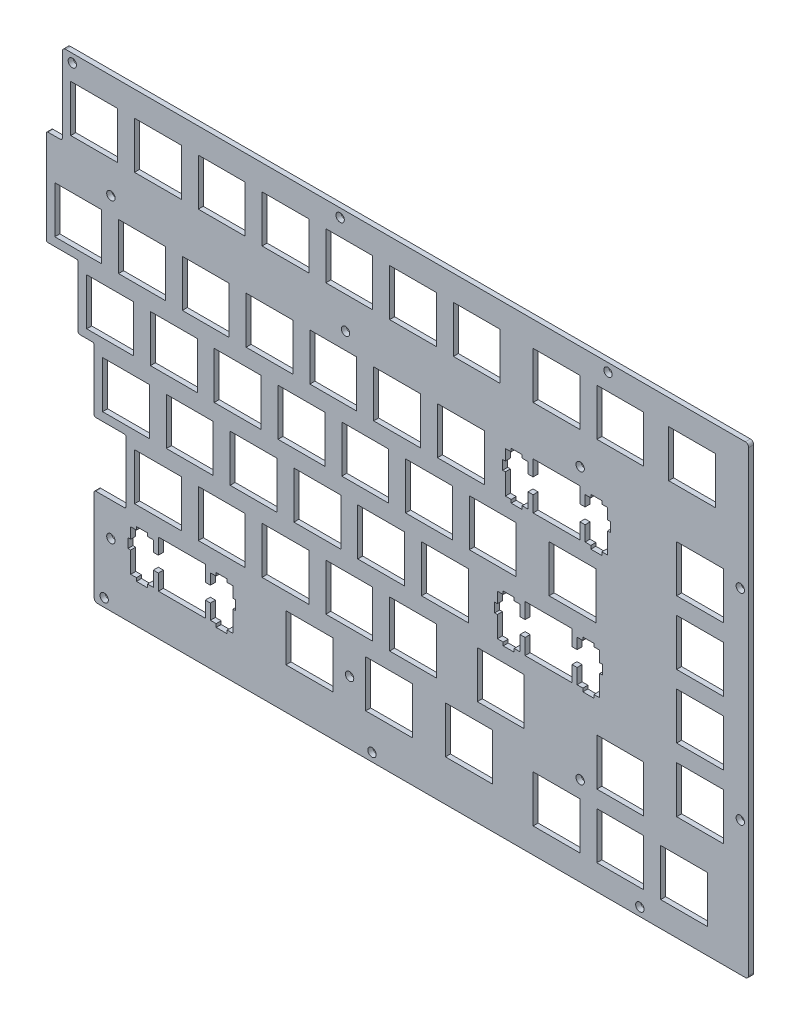
SolidWorks part; units mm, degrees
material "PC 高粘度"
ref_plane "前视基准面" through (0, 0, 0) normal (0, 0, 1) x (1, 0, 0)
ref_plane "上视基准面" through (0, 0, 0) normal (0, 1, 0) x (1, 0, 0)
ref_plane "右视基准面" through (0, 0, 0) normal (1, 0, 0) x (0, 0, -1)
other "Configuration Table"
sketch "Model" plane through (0, 0, 0) normal (0, 0, 1) x (1, 0, 0)
  line L0 (4.8569, 129.021) -> (204.883, 129.021)
  line L1 (204.883, 129.021) -> (204.883, 0.4341)
  line L2 (204.883, 0.4341) -> (14.3819, 0.4341)
  line L3 (21.3817, 112.498) -> (7.3822, 126.497) construction
  line L4 (145.495, 16.9595) -> (159.494, 16.9595)
  line L5 (159.494, 16.9595) -> (159.494, 2.96)
  line L6 (159.494, 2.96) -> (145.495, 2.96)
  line L7 (145.495, 2.96) -> (145.495, 16.9595)
  line L8 (164.545, 16.9595) -> (178.544, 16.9595)
  line L9 (178.544, 16.9595) -> (178.544, 2.96)
  line L10 (178.544, 2.96) -> (164.545, 2.96)
  line L11 (164.545, 2.96) -> (164.545, 16.9595)
  line L12 (183.595, 16.9595) -> (197.594, 16.9595)
  line L13 (197.594, 16.9595) -> (197.594, 2.96)
  line L14 (197.594, 2.96) -> (183.595, 2.96)
  line L15 (183.595, 2.96) -> (183.595, 16.9595)
  line L16 (33.5759, 21.722) -> (33.5759, 17.0215)
  line L17 (33.5759, 17.0215) -> (32.0504, 17.0215)
  line L18 (32.0504, 17.0215) -> (32.0504, 20.2517)
  line L19 (32.0504, 20.2517) -> (30.3251, 20.2517)
  line L20 (30.3251, 20.2517) -> (30.3251, 21.1722)
  line L21 (30.3251, 21.1722) -> (27.0261, 21.1722)
  line L22 (27.0261, 21.1722) -> (27.0261, 20.2517)
  line L23 (27.0261, 20.2517) -> (25.3008, 20.2517)
  line L24 (25.3008, 20.2517) -> (25.3008, 17.0215)
  line L25 (25.3008, 17.0215) -> (24.4753, 17.0215)
  line L26 (24.4753, 17.0215) -> (24.4753, 14.2227)
  line L27 (24.4753, 14.2227) -> (25.3008, 14.2227)
  line L28 (25.3008, 14.2227) -> (25.3008, 7.9527)
  line L29 (25.3008, 7.9527) -> (27.0261, 7.9527)
  line L30 (27.0261, 7.9527) -> (27.0261, 6.9729)
  line L31 (27.0261, 6.9729) -> (30.3251, 6.9729)
  line L32 (30.3251, 6.9729) -> (30.3251, 7.9527)
  line L33 (30.3251, 7.9527) -> (32.0504, 7.9527)
  line L34 (32.0504, 7.9527) -> (32.0504, 12.4216)
  line L35 (32.0504, 12.4216) -> (33.5759, 12.4216)
  line L36 (33.5759, 12.4216) -> (33.5759, 7.7225)
  line L37 (33.5759, 7.7225) -> (47.5753, 7.7225)
  line L38 (47.5753, 7.7225) -> (47.5753, 12.4216)
  line L39 (47.5753, 12.4216) -> (49.101, 12.4216)
  line L40 (49.101, 12.4216) -> (49.101, 7.9527)
  line L41 (49.101, 7.9527) -> (50.8247, 7.9527)
  line L42 (50.8247, 7.9527) -> (50.8247, 6.9729)
  line L43 (50.8247, 6.9729) -> (54.1253, 6.9729)
  line L44 (54.1253, 6.9729) -> (54.1253, 7.9527)
  line L45 (54.1253, 7.9527) -> (55.8504, 7.9527)
  line L46 (55.8504, 7.9527) -> (55.8504, 14.2227)
  line L47 (55.8504, 14.2227) -> (56.6759, 14.2227)
  line L48 (56.6759, 14.2227) -> (56.6759, 17.0215)
  line L49 (56.6759, 17.0215) -> (55.8504, 17.0215)
  line L50 (55.8504, 17.0215) -> (55.8504, 20.2517)
  line L51 (55.8504, 20.2517) -> (54.1253, 20.2517)
  line L52 (54.1253, 20.2517) -> (54.1253, 21.1722)
  line L53 (54.1253, 21.1722) -> (50.8247, 21.1722)
  line L54 (50.8247, 21.1722) -> (50.8247, 20.2517)
  line L55 (50.8247, 20.2517) -> (49.101, 20.2517)
  line L56 (49.101, 20.2517) -> (49.101, 17.0215)
  line L57 (49.101, 17.0215) -> (47.5753, 17.0215)
  line L58 (47.5753, 17.0215) -> (47.5753, 21.722)
  line L59 (47.5753, 21.722) -> (33.5759, 21.722)
  line L60 (71.676, 21.722) -> (85.6753, 21.722)
  line L61 (85.6753, 21.722) -> (85.6753, 7.7225)
  line L62 (85.6753, 7.7225) -> (71.676, 7.7225)
  line L63 (71.676, 7.7225) -> (71.676, 21.722)
  line L64 (95.4871, 21.722) -> (109.488, 21.722)
  line L65 (109.488, 21.722) -> (109.488, 7.7225)
  line L66 (109.488, 7.7225) -> (95.4871, 7.7225)
  line L67 (95.4871, 7.7225) -> (95.4871, 21.722)
  line L68 (119.301, 21.722) -> (133.3, 21.722)
  line L69 (133.3, 21.722) -> (133.3, 7.7225)
  line L70 (133.3, 7.7225) -> (119.301, 7.7225)
  line L71 (119.301, 7.7225) -> (119.301, 21.722)
  line L72 (164.545, 36.0094) -> (178.544, 36.0094)
  line L73 (178.544, 36.0094) -> (178.544, 22.01)
  line L74 (178.544, 22.01) -> (164.545, 22.01)
  line L75 (164.545, 22.01) -> (164.545, 36.0094)
  line L76 (26.4322, 40.7719) -> (40.4315, 40.7719)
  line L77 (40.4315, 40.7719) -> (40.4315, 26.7725)
  line L78 (40.4315, 26.7725) -> (26.4322, 26.7725)
  line L79 (26.4322, 26.7725) -> (26.4322, 40.7719)
  line L80 (45.4822, 40.7719) -> (59.4815, 40.7719)
  line L81 (59.4815, 40.7719) -> (59.4815, 26.7725)
  line L82 (59.4815, 26.7725) -> (45.4822, 26.7725)
  line L83 (45.4822, 26.7725) -> (45.4822, 40.7719)
  line L84 (64.5322, 40.7719) -> (78.5315, 40.7719)
  line L85 (78.5315, 40.7719) -> (78.5315, 26.7725)
  line L86 (78.5315, 26.7725) -> (64.5322, 26.7725)
  line L87 (64.5322, 26.7725) -> (64.5322, 40.7719)
  line L88 (83.5822, 40.7719) -> (97.5815, 40.7719)
  line L89 (97.5815, 40.7719) -> (97.5815, 26.7725)
  line L90 (97.5815, 26.7725) -> (83.5822, 26.7725)
  line L91 (83.5822, 26.7725) -> (83.5822, 40.7719)
  line L92 (102.632, 40.7719) -> (116.632, 40.7719)
  line L93 (116.632, 40.7719) -> (116.632, 26.7725)
  line L94 (116.632, 26.7725) -> (102.632, 26.7725)
  line L95 (102.632, 26.7725) -> (102.632, 40.7719)
  line L96 (128.826, 40.7719) -> (142.825, 40.7719)
  line L97 (142.825, 40.7719) -> (142.825, 26.7725)
  line L98 (142.825, 26.7725) -> (128.826, 26.7725)
  line L99 (128.826, 26.7725) -> (128.826, 40.7719)
  line L100 (188.357, 40.7719) -> (202.357, 40.7719)
  line L101 (202.357, 40.7719) -> (202.357, 26.7725)
  line L102 (202.357, 26.7725) -> (188.357, 26.7725)
  line L103 (188.357, 26.7725) -> (188.357, 40.7719)
  line L104 (143.112, 59.8219) -> (143.112, 55.1215)
  line L105 (143.112, 55.1215) -> (141.588, 55.1215)
  line L106 (141.588, 55.1215) -> (141.588, 58.3516)
  line L107 (141.588, 58.3516) -> (139.863, 58.3516)
  line L108 (139.863, 58.3516) -> (139.863, 59.2723)
  line L109 (139.863, 59.2723) -> (136.562, 59.2723)
  line L110 (136.562, 59.2723) -> (136.562, 58.3516)
  line L111 (136.562, 58.3516) -> (134.837, 58.3516)
  line L112 (134.837, 58.3516) -> (134.837, 55.1215)
  line L113 (134.837, 55.1215) -> (134.013, 55.1215)
  line L114 (134.013, 55.1215) -> (134.013, 52.3226)
  line L115 (134.013, 52.3226) -> (134.837, 52.3226)
  line L116 (134.837, 52.3226) -> (134.837, 46.0527)
  line L117 (134.837, 46.0527) -> (136.562, 46.0527)
  line L118 (136.562, 46.0527) -> (136.562, 45.0716)
  line L119 (136.562, 45.0716) -> (139.863, 45.0716)
  line L120 (139.863, 45.0716) -> (139.863, 46.0527)
  line L121 (139.863, 46.0527) -> (141.588, 46.0527)
  line L122 (141.588, 46.0527) -> (141.588, 50.5217)
  line L123 (141.588, 50.5217) -> (143.112, 50.5217)
  line L124 (143.112, 50.5217) -> (143.112, 45.8227)
  line L125 (143.112, 45.8227) -> (157.113, 45.8227)
  line L126 (157.113, 45.8227) -> (157.113, 50.5217)
  line L127 (157.113, 50.5217) -> (158.637, 50.5217)
  line L128 (158.637, 50.5217) -> (158.637, 46.0527)
  line L129 (158.637, 46.0527) -> (160.362, 46.0527)
  line L130 (160.362, 46.0527) -> (160.362, 45.0716)
  line L131 (160.362, 45.0716) -> (163.663, 45.0716)
  line L132 (163.663, 45.0716) -> (163.663, 46.0527)
  line L133 (163.663, 46.0527) -> (165.388, 46.0527)
  line L134 (165.388, 46.0527) -> (165.388, 52.3226)
  line L135 (165.388, 52.3226) -> (166.212, 52.3226)
  line L136 (166.212, 52.3226) -> (166.212, 55.1215)
  line L137 (166.212, 55.1215) -> (165.388, 55.1215)
  line L138 (165.388, 55.1215) -> (165.388, 58.3516)
  line L139 (165.388, 58.3516) -> (163.663, 58.3516)
  line L140 (163.663, 58.3516) -> (163.663, 59.2723)
  line L141 (163.663, 59.2723) -> (160.362, 59.2723)
  line L142 (160.362, 59.2723) -> (160.362, 58.3516)
  line L143 (160.362, 58.3516) -> (158.637, 58.3516)
  line L144 (158.637, 58.3516) -> (158.637, 55.1215)
  line L145 (158.637, 55.1215) -> (157.113, 55.1215)
  line L146 (157.113, 55.1215) -> (157.113, 59.8219)
  line L147 (157.113, 59.8219) -> (143.112, 59.8219)
  line L148 (16.9072, 59.8219) -> (30.9066, 59.8219)
  line L149 (30.9066, 59.8219) -> (30.9066, 45.8227)
  line L150 (30.9066, 45.8227) -> (16.9072, 45.8227)
  line L151 (16.9072, 45.8227) -> (16.9072, 59.8219)
  line L152 (35.9572, 59.8219) -> (49.9565, 59.8219)
  line L153 (49.9565, 59.8219) -> (49.9565, 45.8227)
  line L154 (49.9565, 45.8227) -> (35.9572, 45.8227)
  line L155 (35.9572, 45.8227) -> (35.9572, 59.8219)
  line L156 (55.0072, 59.8219) -> (69.0065, 59.8219)
  line L157 (69.0065, 59.8219) -> (69.0065, 45.8227)
  line L158 (69.0065, 45.8227) -> (55.0072, 45.8227)
  line L159 (55.0072, 45.8227) -> (55.0072, 59.8219)
  line L160 (74.0572, 59.8219) -> (88.0565, 59.8219)
  line L161 (88.0565, 59.8219) -> (88.0565, 45.8227)
  line L162 (88.0565, 45.8227) -> (74.0572, 45.8227)
  line L163 (74.0572, 45.8227) -> (74.0572, 59.8219)
  line L164 (93.1072, 59.8219) -> (107.107, 59.8219)
  line L165 (107.107, 59.8219) -> (107.107, 45.8227)
  line L166 (107.107, 45.8227) -> (93.1072, 45.8227)
  line L167 (93.1072, 45.8227) -> (93.1072, 59.8219)
  line L168 (112.157, 59.8219) -> (126.157, 59.8219)
  line L169 (126.157, 59.8219) -> (126.157, 45.8227)
  line L170 (126.157, 45.8227) -> (112.157, 45.8227)
  line L171 (112.157, 45.8227) -> (112.157, 59.8219)
  line L172 (188.357, 59.8219) -> (202.357, 59.8219)
  line L173 (202.357, 59.8219) -> (202.357, 45.8227)
  line L174 (202.357, 45.8227) -> (188.357, 45.8227)
  line L175 (188.357, 45.8227) -> (188.357, 59.8219)
  line L176 (12.1447, 78.8719) -> (26.1441, 78.8719)
  line L177 (26.1441, 78.8719) -> (26.1441, 64.8727)
  line L178 (26.1441, 64.8727) -> (12.1447, 64.8727)
  line L179 (12.1447, 64.8727) -> (12.1447, 78.8719)
  line L180 (31.1947, 78.8719) -> (45.194, 78.8719)
  line L181 (45.194, 78.8719) -> (45.194, 64.8727)
  line L182 (45.194, 64.8727) -> (31.1947, 64.8727)
  line L183 (31.1947, 64.8727) -> (31.1947, 78.8719)
  line L184 (50.2447, 78.8719) -> (64.244, 78.8719)
  line L185 (64.244, 78.8719) -> (64.244, 64.8727)
  line L186 (64.244, 64.8727) -> (50.2447, 64.8727)
  line L187 (50.2447, 64.8727) -> (50.2447, 78.8719)
  line L188 (69.2947, 78.8719) -> (83.294, 78.8719)
  line L189 (83.294, 78.8719) -> (83.294, 64.8727)
  line L190 (83.294, 64.8727) -> (69.2947, 64.8727)
  line L191 (69.2947, 64.8727) -> (69.2947, 78.8719)
  line L192 (88.3447, 78.8719) -> (102.344, 78.8719)
  line L193 (102.344, 78.8719) -> (102.344, 64.8727)
  line L194 (102.344, 64.8727) -> (88.3447, 64.8727)
  line L195 (88.3447, 64.8727) -> (88.3447, 78.8719)
  line L196 (107.395, 78.8719) -> (121.394, 78.8719)
  line L197 (121.394, 78.8719) -> (121.394, 64.8727)
  line L198 (121.394, 64.8727) -> (107.395, 64.8727)
  line L199 (107.395, 64.8727) -> (107.395, 78.8719)
  line L200 (126.445, 78.8719) -> (140.444, 78.8719)
  line L201 (140.444, 78.8719) -> (140.444, 64.8727)
  line L202 (140.444, 64.8727) -> (126.445, 64.8727)
  line L203 (126.445, 64.8727) -> (126.445, 78.8719)
  line L204 (150.257, 78.8719) -> (164.257, 78.8719)
  line L205 (164.257, 78.8719) -> (164.257, 64.8727)
  line L206 (164.257, 64.8727) -> (150.257, 64.8727)
  line L207 (150.257, 64.8727) -> (150.257, 78.8719)
  line L208 (188.357, 78.8719) -> (202.357, 78.8719)
  line L209 (202.357, 78.8719) -> (202.357, 64.8727)
  line L210 (202.357, 64.8727) -> (188.357, 64.8727)
  line L211 (188.357, 64.8727) -> (188.357, 78.8719)
  line L212 (145.493, 97.9219) -> (145.493, 93.2215)
  line L213 (145.493, 93.2215) -> (143.969, 93.2215)
  line L214 (143.969, 93.2215) -> (143.969, 96.4516)
  line L215 (143.969, 96.4516) -> (142.244, 96.4516)
  line L216 (142.244, 96.4516) -> (142.244, 97.3723)
  line L217 (142.244, 97.3723) -> (138.943, 97.3723)
  line L218 (138.943, 97.3723) -> (138.943, 96.4516)
  line L219 (138.943, 96.4516) -> (137.218, 96.4516)
  line L220 (137.218, 96.4516) -> (137.218, 93.2215)
  line L221 (137.218, 93.2215) -> (136.394, 93.2215)
  line L222 (136.394, 93.2215) -> (136.394, 90.4226)
  line L223 (136.394, 90.4226) -> (137.218, 90.4226)
  line L224 (137.218, 90.4226) -> (137.218, 84.1527)
  line L225 (137.218, 84.1527) -> (138.943, 84.1527)
  line L226 (138.943, 84.1527) -> (138.943, 83.1716)
  line L227 (138.943, 83.1716) -> (142.244, 83.1716)
  line L228 (142.244, 83.1716) -> (142.244, 84.1527)
  line L229 (142.244, 84.1527) -> (143.969, 84.1527)
  line L230 (143.969, 84.1527) -> (143.969, 88.6217)
  line L231 (143.969, 88.6217) -> (145.493, 88.6217)
  line L232 (145.493, 88.6217) -> (145.493, 83.9227)
  line L233 (145.493, 83.9227) -> (159.494, 83.9227)
  line L234 (159.494, 83.9227) -> (159.494, 88.6217)
  line L235 (159.494, 88.6217) -> (161.018, 88.6217)
  line L236 (161.018, 88.6217) -> (161.018, 84.1527)
  line L237 (161.018, 84.1527) -> (162.743, 84.1527)
  line L238 (162.743, 84.1527) -> (162.743, 83.1716)
  line L239 (162.743, 83.1716) -> (166.044, 83.1716)
  line L240 (166.044, 83.1716) -> (166.044, 84.1527)
  line L241 (166.044, 84.1527) -> (167.768, 84.1527)
  line L242 (167.768, 84.1527) -> (167.768, 90.4226)
  line L243 (167.768, 90.4226) -> (168.593, 90.4226)
  line L244 (168.593, 90.4226) -> (168.593, 93.2215)
  line L245 (168.593, 93.2215) -> (167.768, 93.2215)
  line L246 (167.768, 93.2215) -> (167.768, 96.4516)
  line L247 (167.768, 96.4516) -> (166.044, 96.4516)
  line L248 (166.044, 96.4516) -> (166.044, 97.3723)
  line L249 (166.044, 97.3723) -> (162.743, 97.3723)
  line L250 (162.743, 97.3723) -> (162.743, 96.4516)
  line L251 (162.743, 96.4516) -> (161.018, 96.4516)
  line L252 (161.018, 96.4516) -> (161.018, 93.2215)
  line L253 (161.018, 93.2215) -> (159.494, 93.2215)
  line L254 (159.494, 93.2215) -> (159.494, 97.9219)
  line L255 (159.494, 97.9219) -> (145.493, 97.9219)
  line L256 (2.6197, 97.9219) -> (16.6192, 97.9219)
  line L257 (16.6192, 97.9219) -> (16.6192, 83.9227)
  line L258 (16.6192, 83.9227) -> (2.6197, 83.9227)
  line L259 (2.6197, 83.9227) -> (2.6197, 97.9219)
  line L260 (21.6697, 97.9219) -> (35.669, 97.9219)
  line L261 (35.669, 97.9219) -> (35.669, 83.9227)
  line L262 (35.669, 83.9227) -> (21.6697, 83.9227)
  line L263 (21.6697, 83.9227) -> (21.6697, 97.9219)
  line L264 (40.7197, 97.9219) -> (54.719, 97.9219)
  line L265 (54.719, 97.9219) -> (54.719, 83.9227)
  line L266 (54.719, 83.9227) -> (40.7197, 83.9227)
  line L267 (40.7197, 83.9227) -> (40.7197, 97.9219)
  line L268 (59.7697, 97.9219) -> (73.769, 97.9219)
  line L269 (73.769, 97.9219) -> (73.769, 83.9227)
  line L270 (73.769, 83.9227) -> (59.7697, 83.9227)
  line L271 (59.7697, 83.9227) -> (59.7697, 97.9219)
  line L272 (78.8197, 97.9219) -> (92.819, 97.9219)
  line L273 (92.819, 97.9219) -> (92.819, 83.9227)
  line L274 (92.819, 83.9227) -> (78.8197, 83.9227)
  line L275 (78.8197, 83.9227) -> (78.8197, 97.9219)
  line L276 (97.8683, 97.9219) -> (111.869, 97.9219)
  line L277 (111.869, 97.9219) -> (111.869, 83.9227)
  line L278 (111.869, 83.9227) -> (97.8683, 83.9227)
  line L279 (97.8683, 83.9227) -> (97.8683, 97.9219)
  line L280 (116.918, 97.9219) -> (130.919, 97.9219)
  line L281 (130.919, 97.9219) -> (130.919, 83.9227)
  line L282 (130.919, 83.9227) -> (116.918, 83.9227)
  line L283 (116.918, 83.9227) -> (116.918, 97.9219)
  line L284 (188.357, 97.9219) -> (202.357, 97.9219)
  line L285 (202.357, 97.9219) -> (202.357, 83.9227)
  line L286 (202.357, 83.9227) -> (188.357, 83.9227)
  line L287 (188.357, 83.9227) -> (188.357, 97.9219)
  line L288 (7.3822, 126.497) -> (21.3817, 126.497)
  line L289 (21.3817, 126.497) -> (21.3817, 112.498)
  line L290 (21.3817, 112.498) -> (7.3822, 112.498)
  line L291 (7.3822, 112.498) -> (7.3822, 126.497)
  line L292 (26.4322, 126.497) -> (40.4315, 126.497)
  line L293 (40.4315, 126.497) -> (40.4315, 112.498)
  line L294 (40.4315, 112.498) -> (26.4322, 112.498)
  line L295 (26.4322, 112.498) -> (26.4322, 126.497)
  line L296 (45.4822, 126.497) -> (59.4815, 126.497)
  line L297 (59.4815, 126.497) -> (59.4815, 112.498)
  line L298 (59.4815, 112.498) -> (45.4822, 112.498)
  line L299 (45.4822, 112.498) -> (45.4822, 126.497)
  line L300 (64.5322, 126.497) -> (78.5315, 126.497)
  line L301 (78.5315, 126.497) -> (78.5315, 112.498)
  line L302 (78.5315, 112.498) -> (64.5322, 112.498)
  line L303 (64.5322, 112.498) -> (64.5322, 126.497)
  line L304 (83.5822, 126.497) -> (97.5815, 126.497)
  line L305 (97.5815, 126.497) -> (97.5815, 112.498)
  line L306 (97.5815, 112.498) -> (83.5822, 112.498)
  line L307 (83.5822, 112.498) -> (83.5822, 126.497)
  line L308 (102.632, 126.497) -> (116.632, 126.497)
  line L309 (116.632, 126.497) -> (116.632, 112.498)
  line L310 (116.632, 112.498) -> (102.632, 112.498)
  line L311 (102.632, 112.498) -> (102.632, 126.497)
  line L312 (121.682, 126.497) -> (135.682, 126.497)
  line L313 (135.682, 126.497) -> (135.682, 112.498)
  line L314 (135.682, 112.498) -> (121.682, 112.498)
  line L315 (121.682, 112.498) -> (121.682, 126.497)
  line L316 (145.495, 126.497) -> (159.494, 126.497)
  line L317 (159.494, 126.497) -> (159.494, 112.498)
  line L318 (159.494, 112.498) -> (145.495, 112.498)
  line L319 (145.495, 112.498) -> (145.495, 126.497)
  line L320 (164.545, 126.497) -> (178.544, 126.497)
  line L321 (178.544, 126.497) -> (178.544, 112.498)
  line L322 (178.544, 112.498) -> (164.545, 112.498)
  line L323 (164.545, 112.498) -> (164.545, 126.497)
  line L324 (185.976, 126.497) -> (199.975, 126.497)
  line L325 (199.975, 126.497) -> (199.975, 112.498)
  line L326 (199.975, 112.498) -> (185.976, 112.498)
  line L327 (185.976, 112.498) -> (185.976, 126.497)
  line L328 (0.0939, 81.391) -> (0.0939, 109.971)
  line L329 (14.3819, 24.241) -> (14.3819, 0.4341)
  line L435 (0.0939, 109.971) -> (4.8569, 109.971)
  line L436 (4.8569, 109.971) -> (4.8569, 129.021)
  line L437 (0.0939, 81.391) -> (9.6189, 81.391)
  line L438 (9.6189, 81.391) -> (9.6189, 62.341)
  line L439 (9.6189, 62.341) -> (14.3819, 62.341)
  line L440 (14.3819, 62.341) -> (14.3819, 43.291)
  line L441 (14.3819, 43.291) -> (23.9069, 43.291)
  line L442 (23.9069, 43.291) -> (23.9069, 24.241)
  line L443 (23.9069, 24.241) -> (14.3819, 24.241)
  point P328 (14.3819, 119.4975)
  dimension "D1" = 19.05
  dimension "D2" = 4.763
  dimension "D3" = 28.58
  dimension "D4" = 9.525
  dimension "D5" = 9.525
extrude "凸台-拉伸1" add sketch "Model" along normal blind 1.5
sketch "草图1" plane through (0, 0, 1.5) normal (0, 0, 1) x (1, 0, 0)
  line L3 (14.3819, 0.4341) -> (204.883, 0.4341) construction
  line L4 (204.883, 0.4341) -> (204.883, 129.021) construction
  line L5 (204.883, 129.021) -> (4.8569, 129.021) construction
  line L6 (14.3819, -4.5659) -> (209.883, -4.5659)
  line L7 (209.883, -4.5659) -> (209.883, 134.021)
  line L8 (209.883, 134.021) -> (4.8569, 134.021)
  line L9 (14.3819, -4.5659) -> (209.883, -4.5659)
  line L10 (209.883, -4.5659) -> (209.883, 134.021)
  line L11 (209.883, 134.021) -> (4.8569, 134.021)
  line L12 (14.3819, 0.4341) -> (204.883, 0.4341)
  line L13 (204.883, 0.4341) -> (204.883, 129.021)
  line L14 (204.883, 129.021) -> (4.8569, 129.021)
  line L15 (4.8569, 129.021) -> (4.8569, 134.021)
  line L16 (14.3819, -4.5659) -> (14.3819, 0.4341)
  dimension "D1" = 5
extrude "凸台-拉伸2" add sketch "草图1" against normal blind 1.5
sketch "草图2" plane through (0, 0, 1.5) normal (0, 0, 1) x (1, 0, 0)
  line L0 (14.3819, -4.5659) -> (209.883, -4.5659) construction
  line L1 (14.3819, 24.241) -> (14.3819, -4.5659) construction
  line L2 (209.883, 134.021) -> (4.8569, 134.021) construction
  line L3 (4.8569, 134.021) -> (4.8569, 109.971) construction
  circle A0 centre (7.8569, 131.521) radius 1.25
  circle A1 centre (17.3819, -2.0659) radius 1.25
  dimension "D1" = 2.5
  dimension "D4" = 2.5
  dimension "D2" = 2.5
  dimension "D3" = 3
  dimension "D5" = 2.5
  dimension "D6" = 3
extrude "切除-拉伸1" cut sketch "草图2" against normal blind 3
fillet "圆角1" radius 1 4 edges at (14.3819, -4.5659, 0.75) (4.8569, 134.021, 0.75) (209.883, 134.021, 0.75) (209.883, -4.5659, 0.75)
pattern_linear "阵列(线性)1" count 3 spacing 80 along (1, 0, 0) of "切除-拉伸1"
sketch "草图3" plane through (0, 0, 1.5) normal (0, 0, 1) x (1, 0, 0)
  line L0 (209.883, -3.5659) -> (209.883, 133.021) construction
  line L1 (15.3819, -4.5659) -> (208.883, -4.5659) construction
  circle A0 centre (207.383, 35.4341) radius 1.25
  dimension "D1" = 2.5
  dimension "D2" = 2.5
  dimension "D3" = 40
extrude "切除-拉伸2" cut sketch "草图3" against normal blind 3
pattern_linear "阵列(线性)2" count 3 spacing 60 along (0, 1, 0) of "切除-拉伸2"
fillet "圆角2" radius 0.5 10 edges at (14.3819, 24.241, 0.75) (23.9069, 24.241, 0.75) (23.9069, 43.291, 0.75) (14.3819, 43.291, 0.75) (14.3819, 62.341, 0.75) (9.6189, 62.341, 0.75) (9.6189, 81.391, 0.75) (0.0939, 81.391, 0.75) (0.0939, 109.971, 0.75) (4.8569, 109.971, 0.75)
sketch "草图4" plane through (0, 0, 1.5) normal (0, 0, 1) x (1, 0, 0)
  line L0 (164.545, 36.0094) -> (164.545, 22.01) construction
  line L1 (19.3819, 102.9219) -> (159.545, 102.9219) construction
  line L2 (19.3819, 102.9219) -> (19.3819, 14.241) construction
  line L3 (19.3819, 14.241) -> (159.545, 14.241) construction
  line L4 (159.545, 102.9219) -> (159.545, 14.241) construction
  line L5 (14.3819, 23.741) -> (14.3819, -3.5659) construction
  line L6 (35.669, 97.9219) -> (21.6697, 97.9219) construction
  line L7 (23.4069, 24.241) -> (14.8819, 24.241) construction
  line L8 (159.494, 16.9595) -> (145.495, 16.9595) construction
  line L11 (85.6753, 7.7225) -> (85.6753, 21.722) construction
  circle A0 centre (19.3819, 102.9219) radius 1.25
  circle A1 centre (19.3819, 14.241) radius 1.25
  circle A2 centre (159.545, 21.9595) radius 1.25
  circle A3 centre (159.545, 102.9219) radius 1.25
  circle A4 centre (89.4635, 102.9219) radius 1.25
  circle A5 centre (90.6753, 14.241) radius 1.25
  dimension "D3" = 2.5
  dimension "D4" = 5
  dimension "D7" = 5
  dimension "D1" = 5
  dimension "D2" = 5
  dimension "D5" = 10
  dimension "D6" = 5
extrude "切除-拉伸3" cut sketch "草图4" against normal blind 10
